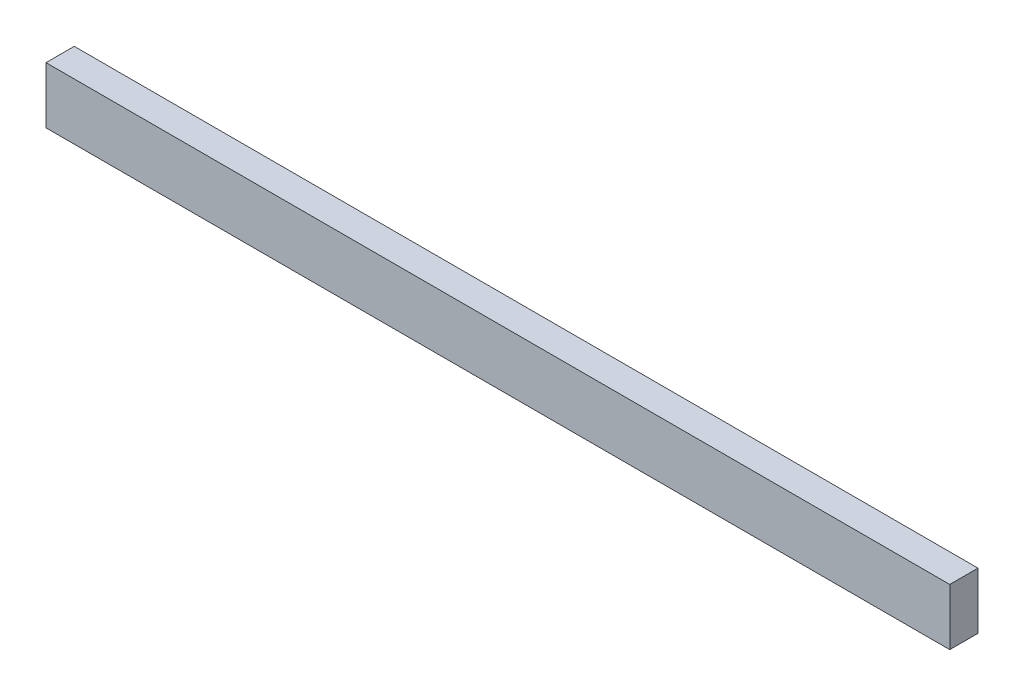
SolidWorks part; units mm, degrees
ref_plane "Front Plane" through (0, 0, 0) normal (0, 0, 1) x (1, 0, 0)
ref_plane "Top Plane" through (0, 0, 0) normal (0, 1, 0) x (1, 0, 0)
ref_plane "Right Plane" through (0, 0, 0) normal (1, 0, 0) x (0, 0, -1)
sketch "Sketch1" plane through (0, 0, 0) normal (0, 0, 1) x (1, 0, 0)
  line L1 (-43.0876, 8.3002) -> (58.5124, 8.3002)
  line L2 (-43.0876, 8.3002) -> (-43.0876, 14.6502)
  line L3 (-43.0876, 14.6502) -> (58.5124, 14.6502)
  line L4 (58.5124, 8.3002) -> (58.5124, 14.6502)
  line L5 (-43.0876, 8.3002) -> (58.5124, 14.6502) construction
  line L6 (-43.0876, 14.6502) -> (58.5124, 8.3002) construction
  point P0 (7.7124, 11.4752)
  dimension "D1" = 101.6
  dimension "D2" = 6.35
extrude "Boss-Extrude1" add sketch "Sketch1" along normal blind 3.175
